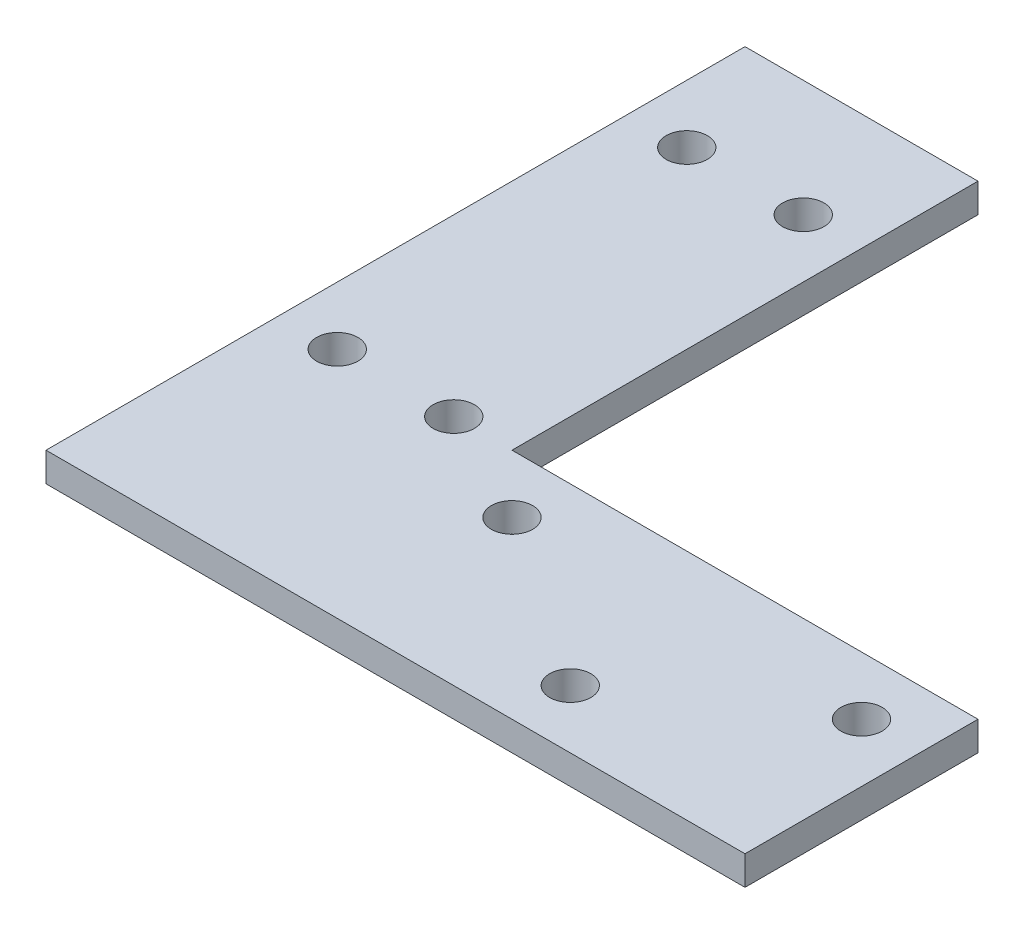
SolidWorks part; units mm, degrees
ref_plane "Front Plane" through (0, 0, 0) normal (0, 0, 1) x (1, 0, 0)
ref_plane "Top Plane" through (0, 0, 0) normal (0, 1, 0) x (1, 0, 0)
ref_plane "Right Plane" through (0, 0, 0) normal (1, 0, 0) x (0, 0, -1)
sketch "Sketch1" plane through (0, 0, 0) normal (0, 1, 0) x (1, 0, 0)
  line L0 (0, 0) -> (76.2, 0)
  line L1 (76.2, 0) -> (76.2, 25.4)
  line L2 (76.2, 25.4) -> (25.4, 25.4)
  line L3 (25.4, 25.4) -> (25.4, 76.2)
  line L4 (25.4, 76.2) -> (0, 76.2)
  line L5 (0, 76.2) -> (0, 0)
  line L6 (31.75, 19.05) -> (69.85, 19.05) construction
  line L7 (50.8, 6.35) -> (50.8, 19.05) construction
  circle A0 centre (31.75, 19.05) radius 2.25
  circle A1 centre (69.85, 19.05) radius 2.25
  circle A2 centre (50.8, 6.35) radius 2.25
  circle A3 centre (19.05, 63.5) radius 2.25
  circle A4 centre (19.05, 25.4) radius 2.25
  circle A5 centre (6.35, 25.4) radius 2.25
  circle A6 centre (6.35, 63.5) radius 2.25
  point P22 (19.7914, 46.0318)
  point P23 (0, 0)
  point P24 (0, 0)
  point P25 (0, 0)
  point P26 (16.156, 6.35)
  point P27 (0, 0)
  point P28 (0, 0)
  dimension "D3" = 4.5
  dimension "D8" = 6.35
  dimension "D1" = 25.4
  dimension "D2" = 76.2
  dimension "D4" = 6.35
  dimension "D5" = 38.1
  dimension "D6" = 6.35
  dimension "D7" = 6.35
  dimension "D9" = 38.1
  dimension "D10" = 38.1
  dimension "D11" = 6.35
  dimension "D12" = 12.7
  dimension "D13" = 25.4
extrude "Boss-Extrude1" add sketch "Sketch1" along normal blind 3.175
